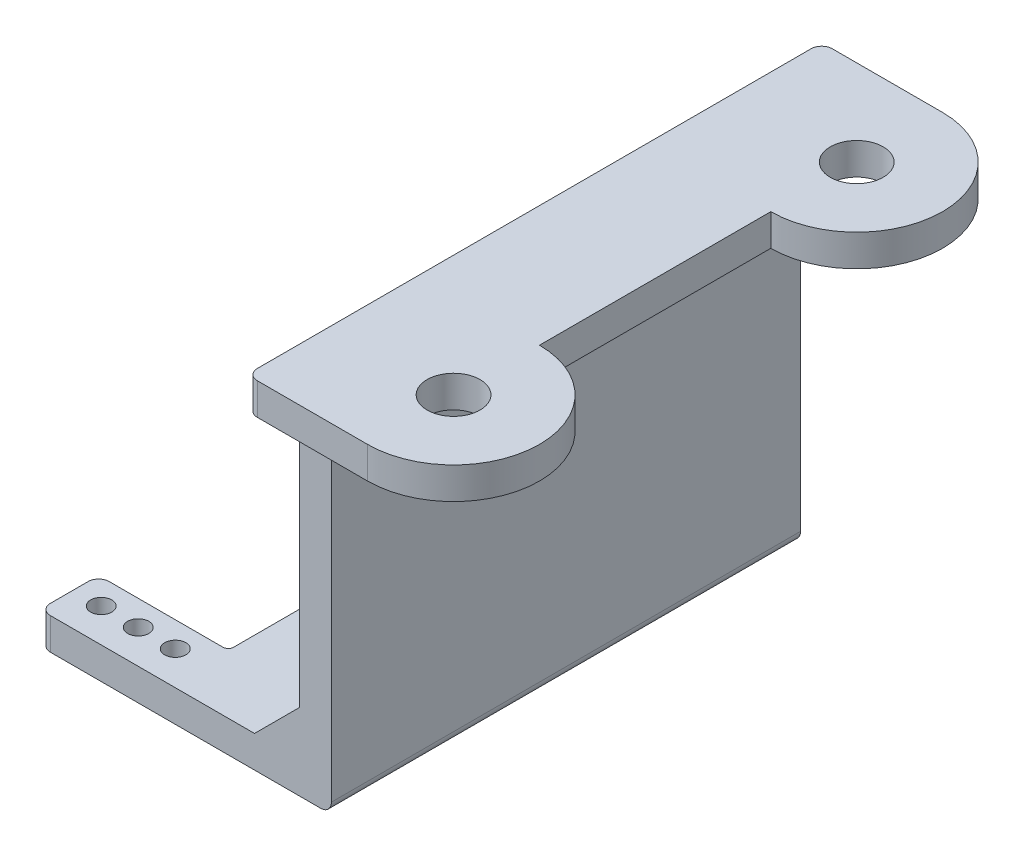
SolidWorks part; units mm, degrees
ref_plane "Front Plane" through (0, 0, 0) normal (0, 0, 1) x (1, 0, 0)
ref_plane "Top Plane" through (0, 0, 0) normal (0, 1, 0) x (1, 0, 0)
ref_plane "Right Plane" through (0, 0, 0) normal (1, 0, 0) x (0, 0, -1)
sketch "Sketch4" plane through (0, 0, 0) normal (0, 1, 0) x (1, 0, 0)
  line L0 (-61.5497, 55.3673) -> (-61.5497, 1.0273)
  line L1 (-61.5497, 55.3673) -> (-50.1197, 55.3673)
  line L2 (-61.5497, 1.0273) -> (-50.1197, 1.0273)
  line L3 (-61.5497, 28.1973) -> (-47.3632, 28.1973) construction
  line L4 (-50.1197, 39.1273) -> (-50.1197, 17.2673)
  arc A0 (-50.1197, 1.0273) -> (-50.1197, 17.2673) centre (-50.1197, 9.1473) ccw
  arc A1 (-50.1197, 55.3673) -> (-50.1197, 39.1273) centre (-50.1197, 47.2473) cw
  circle A2 centre (-50.1197, 47.2473) radius 2.5
  circle A3 centre (-50.1197, 9.1473) radius 2.5
  dimension "D2" = 5
  dimension "D3" = 5
  dimension "D4" = 11.43
  dimension "D5" = 38.1
  dimension "D1" = 54.34
extrude "Boss-Extrude1" add sketch "Sketch4" against normal blind 3
ref_plane "Plane1" through (0, 0, -28.1973) normal (0, 0, 1) x (1, 0, 0)
sketch "Sketch5" plane through (0, -3, 0) normal (0, -1, 0) x (1, 0, 0)
  line L1 (-61.5497, -6.0273) -> (-58.5497, -6.0273)
  line L2 (-61.5497, -6.0273) -> (-61.5497, -50.3673)
  line L3 (-61.5497, -50.3673) -> (-58.5497, -50.3673)
  line L4 (-58.5497, -6.0273) -> (-58.5497, -50.3673)
  line L5 (-61.5497, -1.0273) -> (-50.1197, -1.0273) construction
  line L6 (-50.1197, -55.3673) -> (-61.5497, -55.3673) construction
  dimension "D1" = 3
  dimension "D2" = 5
  dimension "D3" = 5
extrude "Boss-Extrude2" add sketch "Sketch5" along normal blind 34
sketch "Sketch11" plane through (0, -37, 0) normal (0, -1, 0) x (1, 0, 0)
  line L7 (-86.1052, -50.3673) -> (-86.1052, -35.3623)
  line L13 (-61.5497, -32.3229) -> (-61.5497, -32.3223)
  line L29 (-61.5497, -28.1973) -> (-83.8552, -28.1973) construction
  line L30 (-86.1052, -6.0273) -> (-61.5497, -6.0273)
  line L31 (-61.5497, -6.0273) -> (-61.5497, -50.3673) construction
  line L32 (-61.5497, -6.0273) -> (-61.5497, -50.3673)
  line L33 (-61.5497, -50.3673) -> (-86.1052, -50.3673)
  line L35 (-73.8552, -23.4773) -> (-83.8552, -23.4773) construction
  line L36 (-86.1052, -35.3623) -> (-73.8552, -35.3623)
  line L38 (-86.1052, -11.5923) -> (-73.8552, -11.5923)
  line L39 (-73.8552, -35.3623) -> (-73.8552, -11.5923)
  line L40 (-86.1052, -11.5923) -> (-86.1052, -6.0273)
  line L41 (-73.8552, -37.7423) -> (-86.1052, -37.7423) construction
  arc A2 (-61.5497, -32.3229) -> (-61.5497, -32.3223) centre (-63.5497, -32.3226) ccw
  circle A8 centre (-76.4852, -37.7423) radius 1
  circle A9 centre (-79.9852, -37.7423) radius 1
  circle A10 centre (-83.4852, -37.7423) radius 1
  circle A11 centre (-83.4852, -9.2123) radius 1
  circle A12 centre (-79.9852, -9.2123) radius 1
  circle A13 centre (-76.4852, -9.2123) radius 1
  dimension "D5" = 2
  dimension "D6" = 2
  dimension "D7" = 2
  dimension "D8" = 2.63
  dimension "D9" = 3.5
  dimension "D10" = 3.5
  dimension "D1" = 4.72
  dimension "D2" = 12.25
  dimension "D3" = 23.77
  dimension "D4" = 2.38
extrude "Boss-Extrude3" add sketch "Sketch11" against normal blind 3
sketch "Sketch15" plane through (0, 0, -28.1973) normal (0, 0, 1) x (1, 0, 0)
  line L0 (-58.5497, -8.1858) -> (-50.1197, -3)
  line L1 (-58.5497, -37) -> (-58.5497, -3) construction
rib "Rib7" sketch "Sketch15" sketch "Sketch15" thickness 2 extrusion direction parallel to sketch draft on no parameters "D1"=2
pattern_linear "LPattern2" count 3 spacing 4 along (0, 0, -1) count 3 spacing 4 along (0, 0, 1) of "Rib7"
sketch "Sketch16" plane through (0, 0, -6.0273) normal (0, 0, 1) x (1, 0, 0)
  line L0 (-65.8108, -34) -> (-61.5497, -29.7389)
  line L1 (-61.5497, -34) -> (-61.5497, -3) construction
  line L2 (-86.1052, -34) -> (-61.5497, -34) construction
rib "Rib8" sketch "Sketch16" sketch "Sketch16" thickness 10 extrusion direction parallel to sketch draft on no parameters "D1"=10
mirror "Mirror1" about plane through (0, 0, -28.1973) normal (0, 0, 1) of "Rib8"
fillet "Fillet3" radius 1 9 edges at (-60.0497, -3, -50.3673) (-60.0497, -3, -6.0273) (-61.5497, -1.5, -1.0273) (-61.5497, -1.5, -55.3673) (-58.5497, -37, -28.1973) (-86.1052, -35.5, -6.0273) (-86.1052, -35.5, -11.5923) (-86.1052, -35.5, -35.3623) (-86.1052, -35.5, -50.3673)
sketch "Sketch17" plane through (-61.5497, 0, 0) normal (-1, 0, 0) x (0, 0, 1)
  line L0 (-40.3673, -29.7389) -> (-40.3673, -34) construction
  line L1 (-16.0273, -34) -> (-16.0273, -29.7389) construction
  line L2 (-16.0273, -34) -> (-40.3673, -34) construction
  line L3 (-40.3673, -27) -> (-40.3673, -34)
  line L4 (-16.0273, -34) -> (-16.0273, -27)
  line L5 (-16.0273, -34) -> (-40.3673, -34)
  line L6 (-40.3673, -27) -> (-16.0273, -27)
  dimension "D1" = 7
extrude "Cut-Extrude1" cut sketch "Sketch17" against normal blind 2
fillet "Fillet4" radius 0.5 2 edges at (-73.8552, -35.5, -11.5923) (-73.8552, -35.5, -35.3623)
